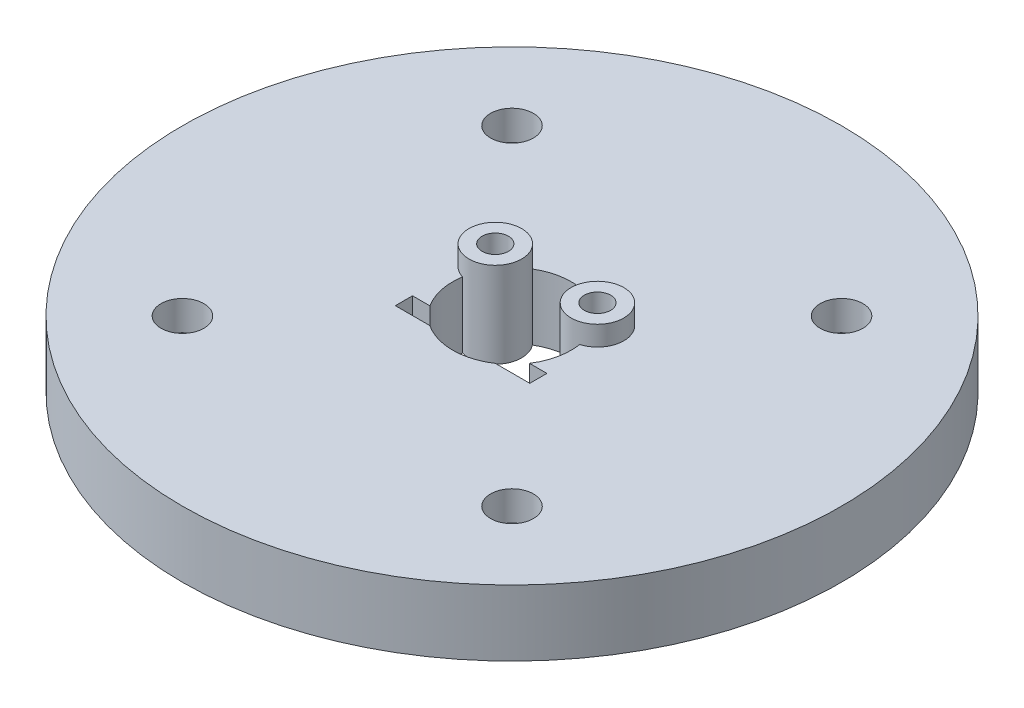
SolidWorks part; units mm, degrees
ref_plane "Ebene vorne" through (0, 0, 0) normal (0, 0, 1) x (1, 0, 0)
ref_plane "Ebene oben" through (0, 0, 0) normal (0, 1, 0) x (1, 0, 0)
ref_plane "Ebene rechts" through (0, 0, 0) normal (1, 0, 0) x (0, 0, -1)
sketch "Skizze1" plane through (0, 0, 0) normal (0, 1, 0) x (1, 0, 0)
  circle A0 centre (0, 0) radius 50
  dimension "D1" = 100
extrude "Aufsatz-Linear austragen1" add sketch "Skizze1" along normal blind 10
sketch "Skizze2" plane through (0, 10, 0) normal (0, 1, 0) x (1, 0, 0)
  line L1 (-25, -25) -> (25, -25) construction
  line L2 (-25, -25) -> (-25, 25) construction
  line L3 (-25, 25) -> (25, 25) construction
  line L4 (25, -25) -> (25, 25) construction
  line L5 (-25, -25) -> (25, 25) construction
  line L6 (-25, 25) -> (25, -25) construction
  circle A0 centre (-25, 25) radius 1.7
  circle A1 centre (25, 25) radius 1.7
  circle A2 centre (25, -25) radius 1.7
  circle A3 centre (-25, -25) radius 1.7
  point P0 (0, 0)
  point P16 (0, 0)
  dimension "D2" = 3.4
  dimension "D1" = 50
  dimension "D3" = 4
extrude "Schnitt-Linear austragen1" cut sketch "Skizze2" against normal up to surface (10 mm away) up to face at (0, 0, 50)
sketch "Skizze3" plane through (0, 10, 0) normal (0, 1, 0) x (1, 0, 0)
  circle A0 centre (-25, 25) radius 3.25
  circle A1 centre (25, 25) radius 3.25
  circle A2 centre (25, -25) radius 3.25
  circle A3 centre (-25, -25) radius 3.25
  point P12 (0, 0)
  dimension "D1" = 6.5
  dimension "D2" = 4
extrude "Schnitt-Linear austragen2" cut sketch "Skizze3" against normal blind 4.5
sketch "Skizze7" plane through (0, 0, 0) normal (0, -1, 0) x (1, 0, 0)
  circle A0 centre (0, 0) radius 9
  dimension "D1" = 18
extrude "Schnitt-Linear austragen5" cut sketch "Skizze7" against normal through all
sketch "Skizze4" plane through (0, 10, 0) normal (0, 1, 0) x (1, 0, 0)
  line L1 (-10.2, -7.5) -> (10.2, -7.5) construction
  line L2 (-10.2, -7.5) -> (-10.2, 7.5) construction
  line L3 (-10.2, 7.5) -> (10.2, 7.5) construction
  line L4 (10.2, -7.5) -> (10.2, 7.5) construction
  line L5 (-10.2, -7.5) -> (10.2, 7.5) construction
  line L6 (-10.2, 7.5) -> (10.2, -7.5) construction
  line L7 (-10.2, -7.5) -> (10.2, -7.5)
  line L8 (-10.2, -7.5) -> (-10.2, -4.9)
  line L9 (-10.2, -4.9) -> (10.2, -4.9)
  line L10 (10.2, -7.5) -> (10.2, -4.9)
  point P0 (0, 0)
  dimension "D1" = 20.4
  dimension "D2" = 15
  dimension "D3" = 2.6
extrude "Schnitt-Linear austragen3" cut sketch "Skizze4" against normal blind 10
sketch "Skizze5" plane through (0, 10, 0) normal (0, 1, 0) x (1, 0, 0)
  line L0 (0, 0) -> (0, 50) construction
  arc A0 (-6.2208, 6.504) -> (-8.3681, 3.3129) centre (-7.75, 5.215) ccw
  arc A1 (8.3681, 3.3129) -> (6.2208, 6.504) centre (7.75, 5.215) ccw
  circle A2 centre (-7.75, 5.215) radius 4
  circle A3 centre (7.75, 5.215) radius 4
  arc A4 (-6.2208, 6.504) -> (-8.3681, 3.3129) centre (0, 0) ccw
  arc A5 (7.5492, -4.9) -> (-7.5492, -4.9) centre (0, 0) ccw construction
  circle A6 centre (0, 0) radius 50 construction
  arc A7 (6.2208, 6.504) -> (8.3681, 3.3129) centre (0, 0) cw
  dimension "D1" = 2
  dimension "D2" = 4
extrude "Aufsatz-Linear austragen2" add sketch "Skizze5" along normal up to surface and the other way up to surface
sketch "Skizze6" plane through (0, 13, 0) normal (0, 1, 0) x (1, 0, 0)
  circle A0 centre (-7.75, 5.215) radius 2
  arc A1 (-6.2208, 6.504) -> (-8.3681, 3.3129) centre (-7.75, 5.215) ccw construction
  circle A12 centre (7.75, 5.215) radius 2
  arc A13 (8.3681, 3.3129) -> (6.2208, 6.504) centre (7.75, 5.215) ccw construction
extrude "Schnitt-Linear austragen4" cut sketch "Skizze6" against normal blind 6
